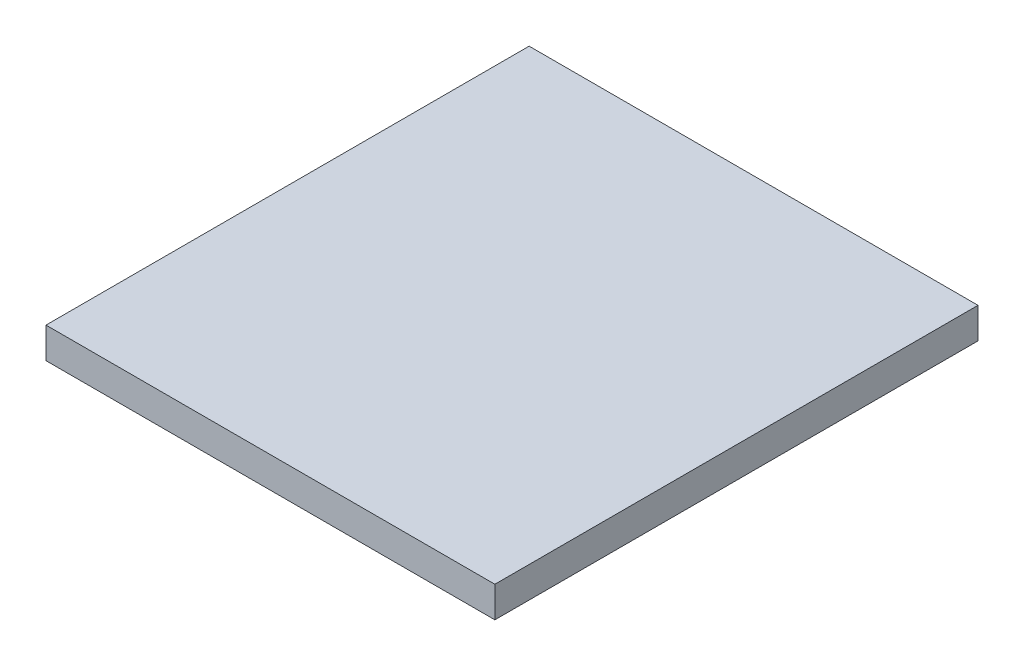
SolidWorks part; units mm, degrees
ref_plane "Спереди" through (0, 0, 0) normal (0, 0, 1) x (1, 0, 0)
ref_plane "Сверху" through (0, 0, 0) normal (0, 1, 0) x (1, 0, 0)
ref_plane "Справа" through (0, 0, 0) normal (1, 0, 0) x (0, 0, -1)
sketch "Эскиз1" plane through (0, 0, 0) normal (0, 1, 0) x (1, 0, 0)
  line L1 (131, -141) -> (-131, -141)
  line L2 (131, -141) -> (131, 141)
  line L3 (131, 141) -> (-131, 141)
  line L4 (-131, -141) -> (-131, 141)
  line L5 (131, -141) -> (-131, 141) construction
  line L6 (131, 141) -> (-131, -141) construction
  point P0 (0, 0)
  dimension "D1" = 262
  dimension "D2" = 282
extrude "Бобышка-Вытянуть1" add sketch "Эскиз1" along normal blind 18
